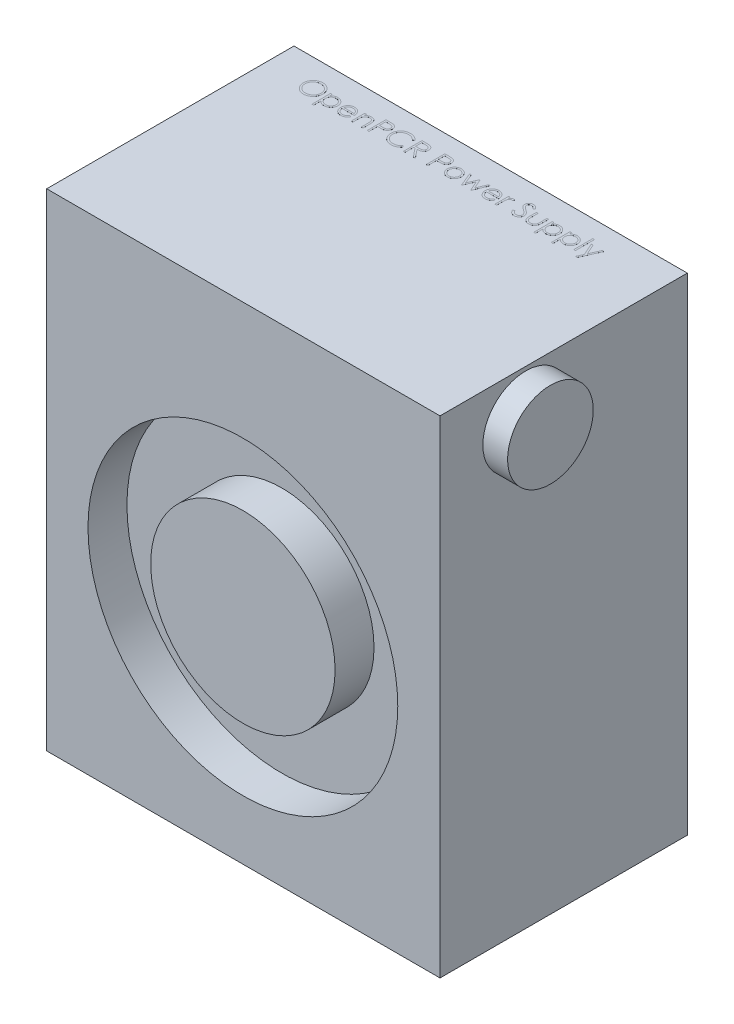
SolidWorks part; units mm, degrees
ref_plane "Front Plane" through (0, 0, 0) normal (0, 0, 1) x (1, 0, 0)
ref_plane "Top Plane" through (0, 0, 0) normal (0, 1, 0) x (1, 0, 0)
ref_plane "Right Plane" through (0, 0, 0) normal (1, 0, 0) x (0, 0, -1)
sketch "Sketch1" plane through (0, 0, 0) normal (0, 1, 0) x (1, 0, 0)
  line L1 (-56.9098, 19.7517) -> (44.0902, 19.7517)
  line L2 (-56.9098, 19.7517) -> (-56.9098, -43.7483)
  line L3 (-56.9098, -43.7483) -> (44.0902, -43.7483)
  line L4 (44.0902, 19.7517) -> (44.0902, -43.7483)
  dimension "D1" = 63.5
  dimension "D2" = 101
extrude "Boss-Extrude1" add sketch "Sketch1" along normal blind 125
sketch "Sketch2" plane through (0, 0, 43.7483) normal (0, 0, 1) x (1, 0, 0)
  line L0 (-56.9098, 0) -> (44.0902, 0) construction
  circle A0 centre (-6.531, 55) radius 14.2966
  circle A1 centre (-6.531, 55) radius 23.6744
  circle A2 centre (-6.531, 55) radius 35.6991
  circle A3 centre (-6.531, 55) radius 39.7724
  dimension "D1" = 55
extrude "Cut-Extrude1" cut sketch "Sketch2" against normal blind 10 contours A1 A0 | A3
hole_wizard "3/16 (0.1875) Diameter Hole2" positions "Sketch6" profile "Sketch5" hole size "3/16" standard "Ansi Inch"
sketch "Sketch6" plane through (-56.9098, 0, 0) normal (-1, 0, 0) x (0, 0, 1)
  line L0 (-19.7517, 125) -> (43.7483, 125) construction
  line L1 (-19.7517, 125) -> (-19.7517, 0) construction
  point P0 (-13.5017, 119.25)
  dimension "D1" = 5.75
  dimension "D2" = 6.25
sketch "Sketch5" plane through (-56.9098, 119.25, -13.5017) normal (0, 1, 0) x (0, 0, 1)
  line L0 (0, 0) -> (0, 14.1308)
  line L1 (0, 14.1308) -> (2.3812, 12.7)
  line L2 (2.3812, 12.7) -> (2.3812, 0)
  line L5 (2.3812, 0) -> (0, 0)
  line L10 (0, 14.1308) -> (-2.3812, 12.7) construction
  line L11 (0, -6.35) -> (0, 107.95) construction
  dimension "Hole Dia." = 4.7625
  dimension "Hole Depth" = 12.7
  dimension "Drill Angle" = 118
pattern_linear "LPattern1" count 2 spacing 51 along (0, 0, 1) count 2 spacing 113.5 along (0, -1, 0) of "3/16 (0.1875) Diameter Hole2"
sketch "Sketch7" plane through (-56.9098, 0, 0) normal (-1, 0, 0) x (0, 0, 1)
  line L0 (-3.5925, 119.6131) -> (0.0084, 119.6131)
  line L1 (-8.5925, 119.6131) -> (-4.9916, 119.6131)
  line L2 (-8.5925, 119.6131) -> (-8.5925, 115.9245)
  line L3 (-8.5925, 115.9245) -> (-4.9916, 115.9245)
  line L4 (-4.9916, 119.6131) -> (-4.9916, 115.9245)
  line L5 (-3.5925, 119.6131) -> (-3.5925, 115.9245)
  line L6 (-3.5925, 115.9245) -> (0.0084, 115.9245)
  line L7 (0.0084, 119.6131) -> (0.0084, 115.9245)
  line L8 (1.4075, 119.6131) -> (5.0084, 119.6131)
  line L9 (1.4075, 119.6131) -> (1.4075, 115.9245)
  line L10 (1.4075, 115.9245) -> (5.0084, 115.9245)
  line L11 (5.0084, 119.6131) -> (5.0084, 115.9245)
  line L12 (6.4075, 119.6131) -> (10.0084, 119.6131)
  line L13 (6.4075, 119.6131) -> (6.4075, 115.9245)
  line L14 (6.4075, 115.9245) -> (10.0084, 115.9245)
  line L15 (10.0084, 119.6131) -> (10.0084, 115.9245)
  line L16 (11.4075, 119.6131) -> (15.0084, 119.6131)
  line L17 (11.4075, 119.6131) -> (11.4075, 115.9245)
  line L18 (11.4075, 115.9245) -> (15.0084, 115.9245)
  line L19 (15.0084, 119.6131) -> (15.0084, 115.9245)
  line L20 (16.4075, 119.6131) -> (20.0084, 119.6131)
  line L21 (16.4075, 119.6131) -> (16.4075, 115.9245)
  line L22 (16.4075, 115.9245) -> (20.0084, 115.9245)
  line L23 (20.0084, 119.6131) -> (20.0084, 115.9245)
  line L24 (21.4075, 119.6131) -> (25.0084, 119.6131)
  line L25 (21.4075, 119.6131) -> (21.4075, 115.9245)
  line L26 (21.4075, 115.9245) -> (25.0084, 115.9245)
  line L27 (25.0084, 119.6131) -> (25.0084, 115.9245)
  line L28 (26.4075, 119.6131) -> (30.0084, 119.6131)
  line L29 (26.4075, 119.6131) -> (26.4075, 115.9245)
  line L30 (26.4075, 115.9245) -> (30.0084, 115.9245)
  line L31 (30.0084, 119.6131) -> (30.0084, 115.9245)
  line L32 (-8.5925, 114.6131) -> (-4.9916, 114.6131)
  line L33 (-8.5925, 114.6131) -> (-8.5925, 110.9245)
  line L34 (-8.5925, 110.9245) -> (-4.9916, 110.9245)
  line L35 (-4.9916, 114.6131) -> (-4.9916, 110.9245)
  line L36 (-3.5925, 114.6131) -> (0.0084, 114.6131)
  line L37 (-3.5925, 114.6131) -> (-3.5925, 110.9245)
  line L38 (-3.5925, 110.9245) -> (0.0084, 110.9245)
  line L39 (0.0084, 114.6131) -> (0.0084, 110.9245)
  line L40 (1.4075, 114.6131) -> (5.0084, 114.6131)
  line L41 (1.4075, 114.6131) -> (1.4075, 110.9245)
  line L42 (1.4075, 110.9245) -> (5.0084, 110.9245)
  line L43 (5.0084, 114.6131) -> (5.0084, 110.9245)
  line L44 (6.4075, 114.6131) -> (10.0084, 114.6131)
  line L45 (6.4075, 114.6131) -> (6.4075, 110.9245)
  line L46 (6.4075, 110.9245) -> (10.0084, 110.9245)
  line L47 (10.0084, 114.6131) -> (10.0084, 110.9245)
  line L48 (11.4075, 114.6131) -> (15.0084, 114.6131)
  line L49 (11.4075, 114.6131) -> (11.4075, 110.9245)
  line L50 (11.4075, 110.9245) -> (15.0084, 110.9245)
  line L51 (15.0084, 114.6131) -> (15.0084, 110.9245)
  line L52 (16.4075, 114.6131) -> (20.0084, 114.6131)
  line L53 (16.4075, 114.6131) -> (16.4075, 110.9245)
  line L54 (16.4075, 110.9245) -> (20.0084, 110.9245)
  line L55 (20.0084, 114.6131) -> (20.0084, 110.9245)
  line L56 (21.4075, 114.6131) -> (25.0084, 114.6131)
  line L57 (21.4075, 114.6131) -> (21.4075, 110.9245)
  line L58 (21.4075, 110.9245) -> (25.0084, 110.9245)
  line L59 (25.0084, 114.6131) -> (25.0084, 110.9245)
  line L60 (26.4075, 114.6131) -> (30.0084, 114.6131)
  line L61 (26.4075, 114.6131) -> (26.4075, 110.9245)
  line L62 (26.4075, 110.9245) -> (30.0084, 110.9245)
  line L63 (30.0084, 114.6131) -> (30.0084, 110.9245)
  line L64 (-8.5925, 109.6131) -> (-4.9916, 109.6131)
  line L65 (-8.5925, 109.6131) -> (-8.5925, 105.9245)
  line L66 (-8.5925, 105.9245) -> (-4.9916, 105.9245)
  line L67 (-4.9916, 109.6131) -> (-4.9916, 105.9245)
  line L68 (-3.5925, 109.6131) -> (0.0084, 109.6131)
  line L69 (-3.5925, 109.6131) -> (-3.5925, 105.9245)
  line L70 (-3.5925, 105.9245) -> (0.0084, 105.9245)
  line L71 (0.0084, 109.6131) -> (0.0084, 105.9245)
  line L72 (1.4075, 109.6131) -> (5.0084, 109.6131)
  line L73 (1.4075, 109.6131) -> (1.4075, 105.9245)
  line L74 (1.4075, 105.9245) -> (5.0084, 105.9245)
  line L75 (5.0084, 109.6131) -> (5.0084, 105.9245)
  line L76 (6.4075, 109.6131) -> (10.0084, 109.6131)
  line L77 (6.4075, 109.6131) -> (6.4075, 105.9245)
  line L78 (6.4075, 105.9245) -> (10.0084, 105.9245)
  line L79 (10.0084, 109.6131) -> (10.0084, 105.9245)
  line L80 (11.4075, 109.6131) -> (15.0084, 109.6131)
  line L81 (11.4075, 109.6131) -> (11.4075, 105.9245)
  line L82 (11.4075, 105.9245) -> (15.0084, 105.9245)
  line L83 (15.0084, 109.6131) -> (15.0084, 105.9245)
  line L84 (16.4075, 109.6131) -> (20.0084, 109.6131)
  line L85 (16.4075, 109.6131) -> (16.4075, 105.9245)
  line L86 (16.4075, 105.9245) -> (20.0084, 105.9245)
  line L87 (20.0084, 109.6131) -> (20.0084, 105.9245)
  line L88 (21.4075, 109.6131) -> (25.0084, 109.6131)
  line L89 (21.4075, 109.6131) -> (21.4075, 105.9245)
  line L90 (21.4075, 105.9245) -> (25.0084, 105.9245)
  line L91 (25.0084, 109.6131) -> (25.0084, 105.9245)
  line L92 (26.4075, 109.6131) -> (30.0084, 109.6131)
  line L93 (26.4075, 109.6131) -> (26.4075, 105.9245)
  line L94 (26.4075, 105.9245) -> (30.0084, 105.9245)
  line L95 (30.0084, 109.6131) -> (30.0084, 105.9245)
  line L96 (-8.5925, 104.6131) -> (-4.9916, 104.6131)
  line L97 (-8.5925, 104.6131) -> (-8.5925, 100.9245)
  line L98 (-8.5925, 100.9245) -> (-4.9916, 100.9245)
  line L99 (-4.9916, 104.6131) -> (-4.9916, 100.9245)
  line L100 (-3.5925, 104.6131) -> (0.0084, 104.6131)
  line L101 (-3.5925, 104.6131) -> (-3.5925, 100.9245)
  line L102 (-3.5925, 100.9245) -> (0.0084, 100.9245)
  line L103 (0.0084, 104.6131) -> (0.0084, 100.9245)
  line L104 (1.4075, 104.6131) -> (5.0084, 104.6131)
  line L105 (1.4075, 104.6131) -> (1.4075, 100.9245)
  line L106 (1.4075, 100.9245) -> (5.0084, 100.9245)
  line L107 (5.0084, 104.6131) -> (5.0084, 100.9245)
  line L108 (6.4075, 104.6131) -> (10.0084, 104.6131)
  line L109 (6.4075, 104.6131) -> (6.4075, 100.9245)
  line L110 (6.4075, 100.9245) -> (10.0084, 100.9245)
  line L111 (10.0084, 104.6131) -> (10.0084, 100.9245)
  line L112 (11.4075, 104.6131) -> (15.0084, 104.6131)
  line L113 (11.4075, 104.6131) -> (11.4075, 100.9245)
  line L114 (11.4075, 100.9245) -> (15.0084, 100.9245)
  line L115 (15.0084, 104.6131) -> (15.0084, 100.9245)
  line L116 (16.4075, 104.6131) -> (20.0084, 104.6131)
  line L117 (16.4075, 104.6131) -> (16.4075, 100.9245)
  line L118 (16.4075, 100.9245) -> (20.0084, 100.9245)
  line L119 (20.0084, 104.6131) -> (20.0084, 100.9245)
  line L120 (21.4075, 104.6131) -> (25.0084, 104.6131)
  line L121 (21.4075, 104.6131) -> (21.4075, 100.9245)
  line L122 (21.4075, 100.9245) -> (25.0084, 100.9245)
  line L123 (25.0084, 104.6131) -> (25.0084, 100.9245)
  line L124 (26.4075, 104.6131) -> (30.0084, 104.6131)
  line L125 (26.4075, 104.6131) -> (26.4075, 100.9245)
  line L126 (26.4075, 100.9245) -> (30.0084, 100.9245)
  line L127 (30.0084, 104.6131) -> (30.0084, 100.9245)
  line L128 (-8.5925, 99.6131) -> (-4.9916, 99.6131)
  line L129 (-8.5925, 99.6131) -> (-8.5925, 95.9245)
  line L130 (-8.5925, 95.9245) -> (-4.9916, 95.9245)
  line L131 (-4.9916, 99.6131) -> (-4.9916, 95.9245)
  line L132 (-3.5925, 99.6131) -> (0.0084, 99.6131)
  line L133 (-3.5925, 99.6131) -> (-3.5925, 95.9245)
  line L134 (-3.5925, 95.9245) -> (0.0084, 95.9245)
  line L135 (0.0084, 99.6131) -> (0.0084, 95.9245)
  line L136 (1.4075, 99.6131) -> (5.0084, 99.6131)
  line L137 (1.4075, 99.6131) -> (1.4075, 95.9245)
  line L138 (1.4075, 95.9245) -> (5.0084, 95.9245)
  line L139 (5.0084, 99.6131) -> (5.0084, 95.9245)
  line L140 (6.4075, 99.6131) -> (10.0084, 99.6131)
  line L141 (6.4075, 99.6131) -> (6.4075, 95.9245)
  line L142 (6.4075, 95.9245) -> (10.0084, 95.9245)
  line L143 (10.0084, 99.6131) -> (10.0084, 95.9245)
  line L144 (11.4075, 99.6131) -> (15.0084, 99.6131)
  line L145 (11.4075, 99.6131) -> (11.4075, 95.9245)
  line L146 (11.4075, 95.9245) -> (15.0084, 95.9245)
  line L147 (15.0084, 99.6131) -> (15.0084, 95.9245)
  line L148 (16.4075, 99.6131) -> (20.0084, 99.6131)
  line L149 (16.4075, 99.6131) -> (16.4075, 95.9245)
  line L150 (16.4075, 95.9245) -> (20.0084, 95.9245)
  line L151 (20.0084, 99.6131) -> (20.0084, 95.9245)
  line L152 (21.4075, 99.6131) -> (25.0084, 99.6131)
  line L153 (21.4075, 99.6131) -> (21.4075, 95.9245)
  line L154 (21.4075, 95.9245) -> (25.0084, 95.9245)
  line L155 (25.0084, 99.6131) -> (25.0084, 95.9245)
  line L156 (26.4075, 99.6131) -> (30.0084, 99.6131)
  line L157 (26.4075, 99.6131) -> (26.4075, 95.9245)
  line L158 (26.4075, 95.9245) -> (30.0084, 95.9245)
  line L159 (30.0084, 99.6131) -> (30.0084, 95.9245)
  line L160 (-8.5925, 94.6131) -> (-4.9916, 94.6131)
  line L161 (-8.5925, 94.6131) -> (-8.5925, 90.9245)
  line L162 (-8.5925, 90.9245) -> (-4.9916, 90.9245)
  line L163 (-4.9916, 94.6131) -> (-4.9916, 90.9245)
  line L164 (-3.5925, 94.6131) -> (0.0084, 94.6131)
  line L165 (-3.5925, 94.6131) -> (-3.5925, 90.9245)
  line L166 (-3.5925, 90.9245) -> (0.0084, 90.9245)
  line L167 (0.0084, 94.6131) -> (0.0084, 90.9245)
  line L168 (1.4075, 94.6131) -> (5.0084, 94.6131)
  line L169 (1.4075, 94.6131) -> (1.4075, 90.9245)
  line L170 (1.4075, 90.9245) -> (5.0084, 90.9245)
  line L171 (5.0084, 94.6131) -> (5.0084, 90.9245)
  line L172 (6.4075, 94.6131) -> (10.0084, 94.6131)
  line L173 (6.4075, 94.6131) -> (6.4075, 90.9245)
  line L174 (6.4075, 90.9245) -> (10.0084, 90.9245)
  line L175 (10.0084, 94.6131) -> (10.0084, 90.9245)
  line L176 (11.4075, 94.6131) -> (15.0084, 94.6131)
  line L177 (11.4075, 94.6131) -> (11.4075, 90.9245)
  line L178 (11.4075, 90.9245) -> (15.0084, 90.9245)
  line L179 (15.0084, 94.6131) -> (15.0084, 90.9245)
  line L180 (16.4075, 94.6131) -> (20.0084, 94.6131)
  line L181 (16.4075, 94.6131) -> (16.4075, 90.9245)
  line L182 (16.4075, 90.9245) -> (20.0084, 90.9245)
  line L183 (20.0084, 94.6131) -> (20.0084, 90.9245)
  line L184 (21.4075, 94.6131) -> (25.0084, 94.6131)
  line L185 (21.4075, 94.6131) -> (21.4075, 90.9245)
  line L186 (21.4075, 90.9245) -> (25.0084, 90.9245)
  line L187 (25.0084, 94.6131) -> (25.0084, 90.9245)
  line L188 (26.4075, 94.6131) -> (30.0084, 94.6131)
  line L189 (26.4075, 94.6131) -> (26.4075, 90.9245)
  line L190 (26.4075, 90.9245) -> (30.0084, 90.9245)
  line L191 (30.0084, 94.6131) -> (30.0084, 90.9245)
  line L192 (-8.5925, 89.6131) -> (-4.9916, 89.6131)
  line L193 (-8.5925, 89.6131) -> (-8.5925, 85.9245)
  line L194 (-8.5925, 85.9245) -> (-4.9916, 85.9245)
  line L195 (-4.9916, 89.6131) -> (-4.9916, 85.9245)
  line L196 (-3.5925, 89.6131) -> (0.0084, 89.6131)
  line L197 (-3.5925, 89.6131) -> (-3.5925, 85.9245)
  line L198 (-3.5925, 85.9245) -> (0.0084, 85.9245)
  line L199 (0.0084, 89.6131) -> (0.0084, 85.9245)
  line L200 (1.4075, 89.6131) -> (5.0084, 89.6131)
  line L201 (1.4075, 89.6131) -> (1.4075, 85.9245)
  line L202 (1.4075, 85.9245) -> (5.0084, 85.9245)
  line L203 (5.0084, 89.6131) -> (5.0084, 85.9245)
  line L204 (6.4075, 89.6131) -> (10.0084, 89.6131)
  line L205 (6.4075, 89.6131) -> (6.4075, 85.9245)
  line L206 (6.4075, 85.9245) -> (10.0084, 85.9245)
  line L207 (10.0084, 89.6131) -> (10.0084, 85.9245)
  line L208 (11.4075, 89.6131) -> (15.0084, 89.6131)
  line L209 (11.4075, 89.6131) -> (11.4075, 85.9245)
  line L210 (11.4075, 85.9245) -> (15.0084, 85.9245)
  line L211 (15.0084, 89.6131) -> (15.0084, 85.9245)
  line L212 (16.4075, 89.6131) -> (20.0084, 89.6131)
  line L213 (16.4075, 89.6131) -> (16.4075, 85.9245)
  line L214 (16.4075, 85.9245) -> (20.0084, 85.9245)
  line L215 (20.0084, 89.6131) -> (20.0084, 85.9245)
  line L216 (21.4075, 89.6131) -> (25.0084, 89.6131)
  line L217 (21.4075, 89.6131) -> (21.4075, 85.9245)
  line L218 (21.4075, 85.9245) -> (25.0084, 85.9245)
  line L219 (25.0084, 89.6131) -> (25.0084, 85.9245)
  line L220 (26.4075, 89.6131) -> (30.0084, 89.6131)
  line L221 (26.4075, 89.6131) -> (26.4075, 85.9245)
  line L222 (26.4075, 85.9245) -> (30.0084, 85.9245)
  line L223 (30.0084, 89.6131) -> (30.0084, 85.9245)
  line L224 (-8.5925, 84.6131) -> (-4.9916, 84.6131)
  line L225 (-8.5925, 84.6131) -> (-8.5925, 80.9245)
  line L226 (-8.5925, 80.9245) -> (-4.9916, 80.9245)
  line L227 (-4.9916, 84.6131) -> (-4.9916, 80.9245)
  line L228 (-3.5925, 84.6131) -> (0.0084, 84.6131)
  line L229 (-3.5925, 84.6131) -> (-3.5925, 80.9245)
  line L230 (-3.5925, 80.9245) -> (0.0084, 80.9245)
  line L231 (0.0084, 84.6131) -> (0.0084, 80.9245)
  line L232 (1.4075, 84.6131) -> (5.0084, 84.6131)
  line L233 (1.4075, 84.6131) -> (1.4075, 80.9245)
  line L234 (1.4075, 80.9245) -> (5.0084, 80.9245)
  line L235 (5.0084, 84.6131) -> (5.0084, 80.9245)
  line L236 (6.4075, 84.6131) -> (10.0084, 84.6131)
  line L237 (6.4075, 84.6131) -> (6.4075, 80.9245)
  line L238 (6.4075, 80.9245) -> (10.0084, 80.9245)
  line L239 (10.0084, 84.6131) -> (10.0084, 80.9245)
  line L240 (11.4075, 84.6131) -> (15.0084, 84.6131)
  line L241 (11.4075, 84.6131) -> (11.4075, 80.9245)
  line L242 (11.4075, 80.9245) -> (15.0084, 80.9245)
  line L243 (15.0084, 84.6131) -> (15.0084, 80.9245)
  line L244 (16.4075, 84.6131) -> (20.0084, 84.6131)
  line L245 (16.4075, 84.6131) -> (16.4075, 80.9245)
  line L246 (16.4075, 80.9245) -> (20.0084, 80.9245)
  line L247 (20.0084, 84.6131) -> (20.0084, 80.9245)
  line L248 (21.4075, 84.6131) -> (25.0084, 84.6131)
  line L249 (21.4075, 84.6131) -> (21.4075, 80.9245)
  line L250 (21.4075, 80.9245) -> (25.0084, 80.9245)
  line L251 (25.0084, 84.6131) -> (25.0084, 80.9245)
  line L252 (26.4075, 84.6131) -> (30.0084, 84.6131)
  line L253 (26.4075, 84.6131) -> (26.4075, 80.9245)
  line L254 (26.4075, 80.9245) -> (30.0084, 80.9245)
  line L255 (30.0084, 84.6131) -> (30.0084, 80.9245)
  line L256 (-8.5925, 79.6131) -> (-4.9916, 79.6131)
  line L257 (-8.5925, 79.6131) -> (-8.5925, 75.9245)
  line L258 (-8.5925, 75.9245) -> (-4.9916, 75.9245)
  line L259 (-4.9916, 79.6131) -> (-4.9916, 75.9245)
  line L260 (-3.5925, 79.6131) -> (0.0084, 79.6131)
  line L261 (-3.5925, 79.6131) -> (-3.5925, 75.9245)
  line L262 (-3.5925, 75.9245) -> (0.0084, 75.9245)
  line L263 (0.0084, 79.6131) -> (0.0084, 75.9245)
  line L264 (1.4075, 79.6131) -> (5.0084, 79.6131)
  line L265 (1.4075, 79.6131) -> (1.4075, 75.9245)
  line L266 (1.4075, 75.9245) -> (5.0084, 75.9245)
  line L267 (5.0084, 79.6131) -> (5.0084, 75.9245)
  line L268 (6.4075, 79.6131) -> (10.0084, 79.6131)
  line L269 (6.4075, 79.6131) -> (6.4075, 75.9245)
  line L270 (6.4075, 75.9245) -> (10.0084, 75.9245)
  line L271 (10.0084, 79.6131) -> (10.0084, 75.9245)
  line L272 (11.4075, 79.6131) -> (15.0084, 79.6131)
  line L273 (11.4075, 79.6131) -> (11.4075, 75.9245)
  line L274 (11.4075, 75.9245) -> (15.0084, 75.9245)
  line L275 (15.0084, 79.6131) -> (15.0084, 75.9245)
  line L276 (16.4075, 79.6131) -> (20.0084, 79.6131)
  line L277 (16.4075, 79.6131) -> (16.4075, 75.9245)
  line L278 (16.4075, 75.9245) -> (20.0084, 75.9245)
  line L279 (20.0084, 79.6131) -> (20.0084, 75.9245)
  line L280 (21.4075, 79.6131) -> (25.0084, 79.6131)
  line L281 (21.4075, 79.6131) -> (21.4075, 75.9245)
  line L282 (21.4075, 75.9245) -> (25.0084, 75.9245)
  line L283 (25.0084, 79.6131) -> (25.0084, 75.9245)
  line L284 (26.4075, 79.6131) -> (30.0084, 79.6131)
  line L285 (26.4075, 79.6131) -> (26.4075, 75.9245)
  line L286 (26.4075, 75.9245) -> (30.0084, 75.9245)
  line L287 (30.0084, 79.6131) -> (30.0084, 75.9245)
  line L288 (-8.5925, 74.6131) -> (-4.9916, 74.6131)
  line L289 (-8.5925, 74.6131) -> (-8.5925, 70.9245)
  line L290 (-8.5925, 70.9245) -> (-4.9916, 70.9245)
  line L291 (-4.9916, 74.6131) -> (-4.9916, 70.9245)
  line L292 (-3.5925, 74.6131) -> (0.0084, 74.6131)
  line L293 (-3.5925, 74.6131) -> (-3.5925, 70.9245)
  line L294 (-3.5925, 70.9245) -> (0.0084, 70.9245)
  line L295 (0.0084, 74.6131) -> (0.0084, 70.9245)
  line L296 (1.4075, 74.6131) -> (5.0084, 74.6131)
  line L297 (1.4075, 74.6131) -> (1.4075, 70.9245)
  line L298 (1.4075, 70.9245) -> (5.0084, 70.9245)
  line L299 (5.0084, 74.6131) -> (5.0084, 70.9245)
  line L300 (6.4075, 74.6131) -> (10.0084, 74.6131)
  line L301 (6.4075, 74.6131) -> (6.4075, 70.9245)
  line L302 (6.4075, 70.9245) -> (10.0084, 70.9245)
  line L303 (10.0084, 74.6131) -> (10.0084, 70.9245)
  line L304 (11.4075, 74.6131) -> (15.0084, 74.6131)
  line L305 (11.4075, 74.6131) -> (11.4075, 70.9245)
  line L306 (11.4075, 70.9245) -> (15.0084, 70.9245)
  line L307 (15.0084, 74.6131) -> (15.0084, 70.9245)
  line L308 (16.4075, 74.6131) -> (20.0084, 74.6131)
  line L309 (16.4075, 74.6131) -> (16.4075, 70.9245)
  line L310 (16.4075, 70.9245) -> (20.0084, 70.9245)
  line L311 (20.0084, 74.6131) -> (20.0084, 70.9245)
  line L312 (21.4075, 74.6131) -> (25.0084, 74.6131)
  line L313 (21.4075, 74.6131) -> (21.4075, 70.9245)
  line L314 (21.4075, 70.9245) -> (25.0084, 70.9245)
  line L315 (25.0084, 74.6131) -> (25.0084, 70.9245)
  line L316 (26.4075, 74.6131) -> (30.0084, 74.6131)
  line L317 (26.4075, 74.6131) -> (26.4075, 70.9245)
  line L318 (26.4075, 70.9245) -> (30.0084, 70.9245)
  line L319 (30.0084, 74.6131) -> (30.0084, 70.9245)
  line L320 (31.2983, 109.6498) -> (34.8992, 109.6498)
  line L321 (31.2983, 109.6498) -> (31.2983, 105.9612)
  line L322 (31.2983, 105.9612) -> (34.8992, 105.9612)
  line L323 (34.8992, 109.6498) -> (34.8992, 105.9612)
  line L324 (31.2983, 104.6498) -> (34.8992, 104.6498)
  line L325 (31.2983, 104.6498) -> (31.2983, 100.9612)
  line L326 (31.2983, 100.9612) -> (34.8992, 100.9612)
  line L327 (34.8992, 104.6498) -> (34.8992, 100.9612)
  line L328 (31.2983, 99.6498) -> (34.8992, 99.6498)
  line L329 (31.2983, 99.6498) -> (31.2983, 95.9612)
  line L330 (31.2983, 95.9612) -> (34.8992, 95.9612)
  line L331 (34.8992, 99.6498) -> (34.8992, 95.9612)
  line L332 (31.2983, 94.6498) -> (34.8992, 94.6498)
  line L333 (31.2983, 94.6498) -> (31.2983, 90.9612)
  line L334 (31.2983, 90.9612) -> (34.8992, 90.9612)
  line L335 (34.8992, 94.6498) -> (34.8992, 90.9612)
  line L336 (31.2983, 89.6498) -> (34.8992, 89.6498)
  line L337 (31.2983, 89.6498) -> (31.2983, 85.9612)
  line L338 (31.2983, 85.9612) -> (34.8992, 85.9612)
  line L339 (34.8992, 89.6498) -> (34.8992, 85.9612)
  line L340 (31.2983, 84.6498) -> (34.8992, 84.6498)
  line L341 (31.2983, 84.6498) -> (31.2983, 80.9612)
  line L342 (31.2983, 80.9612) -> (34.8992, 80.9612)
  line L343 (34.8992, 84.6498) -> (34.8992, 80.9612)
  line L344 (31.2983, 79.6498) -> (34.8992, 79.6498)
  line L345 (31.2983, 79.6498) -> (31.2983, 75.9612)
  line L346 (31.2983, 75.9612) -> (34.8992, 75.9612)
  line L347 (34.8992, 79.6498) -> (34.8992, 75.9612)
  line L348 (31.2983, 74.6498) -> (34.8992, 74.6498)
  line L349 (31.2983, 74.6498) -> (31.2983, 70.9612)
  line L350 (31.2983, 70.9612) -> (34.8992, 70.9612)
  line L351 (34.8992, 74.6498) -> (34.8992, 70.9612)
  line L352 (-13.3635, 109.6694) -> (-9.7626, 109.6694)
  line L353 (-13.3635, 109.6694) -> (-13.3635, 105.9808)
  line L354 (-13.3635, 105.9808) -> (-9.7626, 105.9808)
  line L355 (-9.7626, 109.6694) -> (-9.7626, 105.9808)
  line L356 (-13.3635, 104.6694) -> (-9.7626, 104.6694)
  line L357 (-13.3635, 104.6694) -> (-13.3635, 100.9808)
  line L358 (-13.3635, 100.9808) -> (-9.7626, 100.9808)
  line L359 (-9.7626, 104.6694) -> (-9.7626, 100.9808)
  line L360 (-13.3635, 99.6694) -> (-9.7626, 99.6694)
  line L361 (-13.3635, 99.6694) -> (-13.3635, 95.9808)
  line L362 (-13.3635, 95.9808) -> (-9.7626, 95.9808)
  line L363 (-9.7626, 99.6694) -> (-9.7626, 95.9808)
  line L364 (-13.3635, 94.6694) -> (-9.7626, 94.6694)
  line L365 (-13.3635, 94.6694) -> (-13.3635, 90.9808)
  line L366 (-13.3635, 90.9808) -> (-9.7626, 90.9808)
  line L367 (-9.7626, 94.6694) -> (-9.7626, 90.9808)
  line L368 (-13.3635, 89.6694) -> (-9.7626, 89.6694)
  line L369 (-13.3635, 89.6694) -> (-13.3635, 85.9808)
  line L370 (-13.3635, 85.9808) -> (-9.7626, 85.9808)
  line L371 (-9.7626, 89.6694) -> (-9.7626, 85.9808)
  line L372 (-13.3635, 84.6694) -> (-9.7626, 84.6694)
  line L373 (-13.3635, 84.6694) -> (-13.3635, 80.9808)
  line L374 (-13.3635, 80.9808) -> (-9.7626, 80.9808)
  line L375 (-9.7626, 84.6694) -> (-9.7626, 80.9808)
  line L376 (-13.3635, 79.6694) -> (-9.7626, 79.6694)
  line L377 (-13.3635, 79.6694) -> (-13.3635, 75.9808)
  line L378 (-13.3635, 75.9808) -> (-9.7626, 75.9808)
  line L379 (-9.7626, 79.6694) -> (-9.7626, 75.9808)
  line L380 (-13.3635, 74.6694) -> (-9.7626, 74.6694)
  line L381 (-13.3635, 74.6694) -> (-13.3635, 70.9808)
  line L382 (-13.3635, 70.9808) -> (-9.7626, 70.9808)
  line L383 (-9.7626, 74.6694) -> (-9.7626, 70.9808)
  line L384 (31.7438, 70.0389) -> (35.3447, 70.0389)
  line L385 (31.7438, 70.0389) -> (31.7438, 66.3503)
  line L386 (31.7438, 66.3503) -> (35.3447, 66.3503)
  line L387 (35.3447, 70.0389) -> (35.3447, 66.3503)
  line L388 (31.7438, 65.0389) -> (35.3447, 65.0389)
  line L389 (31.7438, 65.0389) -> (31.7438, 61.3503)
  line L390 (31.7438, 61.3503) -> (35.3447, 61.3503)
  line L391 (35.3447, 65.0389) -> (35.3447, 61.3503)
  line L392 (31.7438, 60.0389) -> (35.3447, 60.0389)
  line L393 (31.7438, 60.0389) -> (31.7438, 56.3503)
  line L394 (31.7438, 56.3503) -> (35.3447, 56.3503)
  line L395 (35.3447, 60.0389) -> (35.3447, 56.3503)
  line L396 (31.7438, 55.0389) -> (35.3447, 55.0389)
  line L397 (31.7438, 55.0389) -> (31.7438, 51.3503)
  line L398 (31.7438, 51.3503) -> (35.3447, 51.3503)
  line L399 (35.3447, 55.0389) -> (35.3447, 51.3503)
  line L400 (31.7438, 50.0389) -> (35.3447, 50.0389)
  line L401 (31.7438, 50.0389) -> (31.7438, 46.3503)
  line L402 (31.7438, 46.3503) -> (35.3447, 46.3503)
  line L403 (35.3447, 50.0389) -> (35.3447, 46.3503)
  line L404 (31.7438, 45.0389) -> (35.3447, 45.0389)
  line L405 (31.7438, 45.0389) -> (31.7438, 41.3503)
  line L406 (31.7438, 41.3503) -> (35.3447, 41.3503)
  line L407 (35.3447, 45.0389) -> (35.3447, 41.3503)
  line L408 (31.7438, 40.0389) -> (35.3447, 40.0389)
  line L409 (31.7438, 40.0389) -> (31.7438, 36.3503)
  line L410 (31.7438, 36.3503) -> (35.3447, 36.3503)
  line L411 (35.3447, 40.0389) -> (35.3447, 36.3503)
  line L412 (31.7438, 35.0389) -> (35.3447, 35.0389)
  line L413 (31.7438, 35.0389) -> (31.7438, 31.3503)
  line L414 (31.7438, 31.3503) -> (35.3447, 31.3503)
  line L415 (35.3447, 35.0389) -> (35.3447, 31.3503)
  line L416 (31.7438, 30.0389) -> (35.3447, 30.0389)
  line L417 (31.7438, 30.0389) -> (31.7438, 26.3503)
  line L418 (31.7438, 26.3503) -> (35.3447, 26.3503)
  line L419 (35.3447, 30.0389) -> (35.3447, 26.3503)
  line L420 (31.7438, 25.0389) -> (35.3447, 25.0389)
  line L421 (31.7438, 25.0389) -> (31.7438, 21.3503)
  line L422 (31.7438, 21.3503) -> (35.3447, 21.3503)
  line L423 (35.3447, 25.0389) -> (35.3447, 21.3503)
  line L424 (-13.3435, 69.6011) -> (-9.7427, 69.6011)
  line L425 (-13.3435, 69.6011) -> (-13.3435, 65.9125)
  line L426 (-13.3435, 65.9125) -> (-9.7427, 65.9125)
  line L427 (-9.7427, 69.6011) -> (-9.7427, 65.9125)
  line L428 (-13.3435, 64.6011) -> (-9.7427, 64.6011)
  line L429 (-13.3435, 64.6011) -> (-13.3435, 60.9125)
  line L430 (-13.3435, 60.9125) -> (-9.7427, 60.9125)
  line L431 (-9.7427, 64.6011) -> (-9.7427, 60.9125)
  line L432 (-13.3435, 59.6011) -> (-9.7427, 59.6011)
  line L433 (-13.3435, 59.6011) -> (-13.3435, 55.9125)
  line L434 (-13.3435, 55.9125) -> (-9.7427, 55.9125)
  line L435 (-9.7427, 59.6011) -> (-9.7427, 55.9125)
  line L436 (-13.3435, 54.6011) -> (-9.7427, 54.6011)
  line L437 (-13.3435, 54.6011) -> (-13.3435, 50.9125)
  line L438 (-13.3435, 50.9125) -> (-9.7427, 50.9125)
  line L439 (-9.7427, 54.6011) -> (-9.7427, 50.9125)
  line L440 (-13.3435, 49.6011) -> (-9.7427, 49.6011)
  line L441 (-13.3435, 49.6011) -> (-13.3435, 45.9125)
  line L442 (-13.3435, 45.9125) -> (-9.7427, 45.9125)
  line L443 (-9.7427, 49.6011) -> (-9.7427, 45.9125)
  line L444 (-13.3435, 44.6011) -> (-9.7427, 44.6011)
  line L445 (-13.3435, 44.6011) -> (-13.3435, 40.9125)
  line L446 (-13.3435, 40.9125) -> (-9.7427, 40.9125)
  line L447 (-9.7427, 44.6011) -> (-9.7427, 40.9125)
  line L448 (-13.3435, 39.6011) -> (-9.7427, 39.6011)
  line L449 (-13.3435, 39.6011) -> (-13.3435, 35.9125)
  line L450 (-13.3435, 35.9125) -> (-9.7427, 35.9125)
  line L451 (-9.7427, 39.6011) -> (-9.7427, 35.9125)
  line L452 (-13.3435, 34.6011) -> (-9.7427, 34.6011)
  line L453 (-13.3435, 34.6011) -> (-13.3435, 30.9125)
  line L454 (-13.3435, 30.9125) -> (-9.7427, 30.9125)
  line L455 (-9.7427, 34.6011) -> (-9.7427, 30.9125)
  line L456 (-13.3435, 29.6011) -> (-9.7427, 29.6011)
  line L457 (-13.3435, 29.6011) -> (-13.3435, 25.9125)
  line L458 (-13.3435, 25.9125) -> (-9.7427, 25.9125)
  line L459 (-9.7427, 29.6011) -> (-9.7427, 25.9125)
  line L460 (-13.3435, 24.6011) -> (-9.7427, 24.6011)
  line L461 (-13.3435, 24.6011) -> (-13.3435, 20.9125)
  line L462 (-13.3435, 20.9125) -> (-9.7427, 20.9125)
  line L463 (-9.7427, 24.6011) -> (-9.7427, 20.9125)
  line L464 (26.4779, 70.0389) -> (30.0787, 70.0389)
  line L465 (26.4779, 70.0389) -> (26.4779, 66.3503)
  line L466 (26.4779, 66.3503) -> (30.0787, 66.3503)
  line L467 (30.0787, 70.0389) -> (30.0787, 66.3503)
  line L468 (26.4779, 65.0389) -> (30.0787, 65.0389)
  line L469 (26.4779, 65.0389) -> (26.4779, 61.3503)
  line L470 (26.4779, 61.3503) -> (30.0787, 61.3503)
  line L471 (30.0787, 65.0389) -> (30.0787, 61.3503)
  line L472 (26.4779, 60.0389) -> (30.0787, 60.0389)
  line L473 (26.4779, 60.0389) -> (26.4779, 56.3503)
  line L474 (26.4779, 56.3503) -> (30.0787, 56.3503)
  line L475 (30.0787, 60.0389) -> (30.0787, 56.3503)
  line L476 (26.4779, 55.0389) -> (30.0787, 55.0389)
  line L477 (26.4779, 55.0389) -> (26.4779, 51.3503)
  line L478 (26.4779, 51.3503) -> (30.0787, 51.3503)
  line L479 (30.0787, 55.0389) -> (30.0787, 51.3503)
  line L480 (26.4779, 50.0389) -> (30.0787, 50.0389)
  line L481 (26.4779, 50.0389) -> (26.4779, 46.3503)
  line L482 (26.4779, 46.3503) -> (30.0787, 46.3503)
  line L483 (30.0787, 50.0389) -> (30.0787, 46.3503)
  line L484 (26.4779, 45.0389) -> (30.0787, 45.0389)
  line L485 (26.4779, 45.0389) -> (26.4779, 41.3503)
  line L486 (26.4779, 41.3503) -> (30.0787, 41.3503)
  line L487 (30.0787, 45.0389) -> (30.0787, 41.3503)
  line L488 (26.4779, 40.0389) -> (30.0787, 40.0389)
  line L489 (26.4779, 40.0389) -> (26.4779, 36.3503)
  line L490 (26.4779, 36.3503) -> (30.0787, 36.3503)
  line L491 (30.0787, 40.0389) -> (30.0787, 36.3503)
  line L492 (26.4779, 35.0389) -> (30.0787, 35.0389)
  line L493 (26.4779, 35.0389) -> (26.4779, 31.3503)
  line L494 (26.4779, 31.3503) -> (30.0787, 31.3503)
  line L495 (30.0787, 35.0389) -> (30.0787, 31.3503)
  line L496 (26.4779, 30.0389) -> (30.0787, 30.0389)
  line L497 (26.4779, 30.0389) -> (26.4779, 26.3503)
  line L498 (26.4779, 26.3503) -> (30.0787, 26.3503)
  line L499 (30.0787, 30.0389) -> (30.0787, 26.3503)
  line L500 (26.4779, 25.0389) -> (30.0787, 25.0389)
  line L501 (26.4779, 25.0389) -> (26.4779, 21.3503)
  line L502 (26.4779, 21.3503) -> (30.0787, 21.3503)
  line L503 (30.0787, 25.0389) -> (30.0787, 21.3503)
  dimension "D1" = 8
  dimension "D2" = 10
extrude "Cut-Extrude2" cut sketch "Sketch7" against normal blind 5
sketch "Sketch8" plane through (-56.9098, 0, 0) normal (-1, 0, 0) x (0, 0, 1)
  line L0 (-19.7517, 0) -> (43.7483, 0) construction
  line L1 (-5.5017, 20.3) -> (18.2483, 20.3)
  line L2 (-5.5017, 20.3) -> (-5.5017, 50.95)
  line L3 (-5.5017, 50.95) -> (18.2483, 50.95)
  line L4 (18.2483, 20.3) -> (18.2483, 50.95)
  line L5 (43.7483, 125) -> (43.7483, 0) construction
  line L6 (-19.7517, 125) -> (-19.7517, 0) construction
  line L7 (-19.7517, 125) -> (43.7483, 125) construction
  dimension "D1" = 23.75
  dimension "D2" = 30.65
  dimension "D3" = 20.3
  dimension "D4" = 25.5
  dimension "D5" = 14.25
  dimension "D6" = 74.05
extrude "Power plug" add sketch "Sketch8" along normal blind 3
sketch "Sketch9" plane through (-56.9098, 0, 0) normal (-1, 0, 0) x (0, 0, 1)
  line L0 (18.2483, 50.95) -> (-5.5017, 50.95) construction
  line L1 (-4.4517, 68.35) -> (16.5483, 68.35)
  line L2 (-4.4517, 68.35) -> (-4.4517, 53.35)
  line L3 (-4.4517, 53.35) -> (16.5483, 53.35)
  line L4 (16.5483, 68.35) -> (16.5483, 53.35)
  line L5 (43.7483, 125) -> (43.7483, 0) construction
  line L6 (-19.7517, 125) -> (-19.7517, 0) construction
  dimension "D1" = 15
  dimension "D2" = 21
  dimension "D3" = 2.4
  dimension "D4" = 27.2
  dimension "D5" = 15.3
extrude "Boss-Extrude3" add sketch "Sketch9" along normal blind 2
sketch "Sketch10" plane through (-58.9098, 0, 0) normal (-1, 0, 0) x (0, 0, 1)
  line L1 (-2.0222, 66.0997) -> (13.4778, 66.0997)
  line L2 (-2.0222, 66.0997) -> (-2.0222, 56.0997)
  line L3 (-2.0222, 56.0997) -> (13.4778, 56.0997)
  line L4 (13.4778, 66.0997) -> (13.4778, 56.0997)
  dimension "D1" = 10
  dimension "D2" = 15.5
extrude "Power switch" add sketch "Sketch10" along normal blind 4.3
sketch "Sketch11" plane through (-56.9098, 0, 0) normal (-1, 0, 0) x (0, 0, 1)
  circle A0 centre (-5.647, 12.6107) radius 5
  circle A1 centre (16.3302, 12.6107) radius 5
  dimension "D1" = 10
  dimension "D2" = 10
extrude "Screws" add sketch "Sketch11" along normal blind 1.87
sketch "Sketch12" plane through (44.0902, 0, 0) normal (1, 0, 0) x (0, 0, -1)
  line L0 (-43.7483, 125) -> (-43.7483, 0) construction
  line L1 (-43.7483, 125) -> (19.7517, 125) construction
  circle A0 centre (-21.7483, 113) radius 11
  dimension "D1" = 22
  dimension "D2" = 12
extrude "Boss-Extrude6" add sketch "Sketch12" along normal blind 6.35
sketch "Sketch13" plane through (0, 125, 0) normal (0, 1, 0) x (1, 0, 0)
  line L1 (-56.9098, -43.7483) -> (44.0902, -43.7483)
  line L2 (-56.9098, -43.7483) -> (-56.9098, 19.7517)
  line L3 (-56.9098, 19.7517) -> (44.0902, 19.7517)
  line L4 (44.0902, -43.7483) -> (44.0902, 19.7517)
extrude "Boss-Extrude7" add sketch "Sketch13" along normal blind 0.01
sketch "Sketch14" plane through (-60.1632, 125.01, 5.4248) normal (0, 1, 0) x (1, 0, 0)
  text T0 "OpenPCR Power Supply" font "Century Gothic" height in points 18
extrude "Text" add sketch "Sketch14" along normal blind 0.01
sketch "Sketch15" plane through (-59.9098, 0, 0) normal (-1, 0, 0) x (0, 0, 1)
  line L1 (-4.1875, 49.1905) -> (16.2382, 49.1905)
  line L2 (-4.1875, 49.1905) -> (-4.1875, 22.4162)
  line L3 (-4.1875, 22.4162) -> (16.2382, 22.4162)
  line L4 (16.2382, 49.1905) -> (16.2382, 22.4162)
  circle A0 centre (0, 35.8034) radius 1.3783
  circle A1 centre (9.091, 43.8939) radius 1.4504
  circle A2 centre (9.091, 28.2063) radius 1.6564
extrude "Cut-Extrude3" cut sketch "Sketch15" against normal blind 15
sketch "Sketch16" plane through (-56.9098, 0, 0) normal (-1, 0, 0) x (0, 0, 1)
  line L1 (1.4302, 13.969) -> (10.9559, 13.969)
  line L2 (1.4302, 13.969) -> (1.4302, 17.2714)
  line L3 (1.4302, 17.2714) -> (10.9559, 17.2714)
  line L4 (10.9559, 13.969) -> (10.9559, 17.2714)
extrude "110-230 switch" add sketch "Sketch16" along normal blind 2
